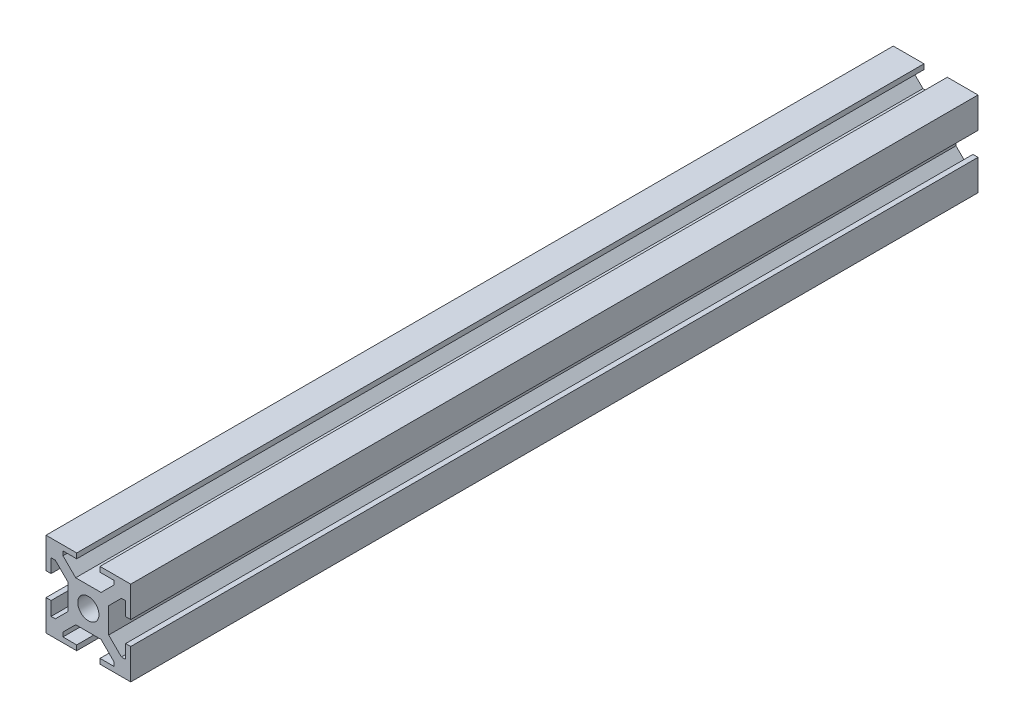
SolidWorks part; units mm, degrees
ref_plane "Plan de face" through (0, 0, 0) normal (0, 0, 1) x (1, 0, 0)
ref_plane "Plan de dessus" through (0, 0, 0) normal (0, 1, 0) x (1, 0, 0)
ref_plane "Plan de droite" through (0, 0, 0) normal (1, 0, 0) x (0, 0, -1)
sketch "Esquisse1" plane through (0, 0, 0) normal (0, 0, 1) x (1, 0, 0)
  line L1 (-22.5051, 0.0904) -> (-2.5051, 0.0904)
  line L2 (-22.5051, 0.0904) -> (-22.5051, -19.9096)
  line L3 (-22.5051, -19.9096) -> (-2.5051, -19.9096)
  line L4 (-2.5051, 0.0904) -> (-2.5051, -19.9096)
  dimension "D1" = 20
  dimension "D2" = 20
extrude "Boss.-Extru.1" add sketch "Esquisse1" along normal blind 200
sketch "Esquisse2" plane through (0, 0, 200) normal (0, 0, 1) x (1, 0, 0)
  line L0 (-22.5051, 0.0904) -> (-22.5051, -19.9096) construction
  line L1 (-22.5051, -7.1596) -> (-21.3051, -7.1596)
  line L2 (-22.5051, -7.1596) -> (-22.5051, -12.6596)
  line L3 (-22.5051, -12.6596) -> (-21.3051, -12.6596)
  line L4 (-21.3051, -7.1596) -> (-21.3051, -12.6596)
  line L5 (-2.5051, 0.0904) -> (-22.5051, 0.0904) construction
  line L6 (-15.2551, 0.0904) -> (-9.7551, 0.0904)
  line L7 (-15.2551, 0.0904) -> (-15.2551, -1.1096)
  line L8 (-15.2551, -1.1096) -> (-9.7551, -1.1096)
  line L9 (-9.7551, 0.0904) -> (-9.7551, -1.1096)
  line L10 (-2.5051, -19.9096) -> (-2.5051, 0.0904) construction
  line L11 (-2.5051, -7.1596) -> (-3.7051, -7.1596)
  line L12 (-2.5051, -7.1596) -> (-2.5051, -12.6596)
  line L13 (-2.5051, -12.6596) -> (-3.7051, -12.6596)
  line L14 (-3.7051, -7.1596) -> (-3.7051, -12.6596)
  line L15 (-22.5051, -19.9096) -> (-2.5051, -19.9096) construction
  line L16 (-15.2551, -19.9096) -> (-9.7551, -19.9096)
  line L17 (-15.2551, -19.9096) -> (-15.2551, -18.7096)
  line L18 (-15.2551, -18.7096) -> (-9.7551, -18.7096)
  line L19 (-9.7551, -19.9096) -> (-9.7551, -18.7096)
  dimension "D1" = 1.2
  dimension "D2" = 1.2
  dimension "D3" = 1.2
  dimension "D4" = 1.2
  dimension "D5" = 5.5
  dimension "D6" = 5.5
  dimension "D7" = 5.5
  dimension "D8" = 5.5
  dimension "D9" = 7.25
  dimension "D10" = 7.25
  dimension "D11" = 7.25
  dimension "D12" = 7.25
extrude "Enlèv. mat.-Extru.1" cut sketch "Esquisse2" against normal through all
sketch "Esquisse3" plane through (0, 0, 200) normal (0, 0, 1) x (1, 0, 0)
  line L0 (-15.2551, 0.0904) -> (-22.5051, 0.0904) construction
  line L1 (-21.3051, -15.9096) -> (-20.3051, -15.9096)
  line L2 (-21.3051, -15.9096) -> (-21.3051, -3.9096)
  line L3 (-21.3051, -3.9096) -> (-20.3051, -3.9096)
  line L4 (-17.3051, -12.9096) -> (-17.3051, -6.9096)
  line L5 (-18.5051, -1.1096) -> (-6.5051, -1.1096)
  line L6 (-18.5051, -1.1096) -> (-18.5051, -2.1096)
  line L7 (-15.5051, -5.1096) -> (-9.5051, -5.1096)
  line L8 (-6.5051, -1.1096) -> (-6.5051, -2.1096)
  line L9 (-3.7051, -3.9096) -> (-4.7051, -3.9096)
  line L10 (-3.7051, -3.9096) -> (-3.7051, -15.9096)
  line L11 (-3.7051, -15.9096) -> (-4.7051, -15.9096)
  line L12 (-7.7051, -6.9096) -> (-7.7051, -12.9096)
  line L13 (-6.5051, -18.7096) -> (-18.5051, -18.7096)
  line L14 (-6.5051, -18.7096) -> (-6.5051, -17.7096)
  line L15 (-9.5051, -14.7096) -> (-15.5051, -14.7096)
  line L16 (-18.5051, -18.7096) -> (-18.5051, -17.7096)
  line L17 (-2.5051, -7.1596) -> (-2.5051, 0.0904) construction
  line L18 (-15.2551, -1.1096) -> (-9.7551, -1.1096) construction
  line L19 (-3.7051, -7.1596) -> (-3.7051, -12.6596) construction
  line L20 (-9.7551, -19.9096) -> (-2.5051, -19.9096) construction
  line L21 (-22.5051, -12.6596) -> (-22.5051, -19.9096) construction
  line L22 (-22.5051, -19.9096) -> (-15.2551, -19.9096) construction
  line L23 (-15.5051, -14.7096) -> (-18.5051, -17.7096)
  line L24 (-20.3051, -15.9096) -> (-17.3051, -12.9096)
  line L25 (-6.5051, -17.7096) -> (-9.5051, -14.7096)
  line L26 (-4.7051, -15.9096) -> (-7.7051, -12.9096)
  line L27 (-4.7051, -3.9096) -> (-7.7051, -6.9096)
  line L28 (-9.5051, -5.1096) -> (-6.5051, -2.1096)
  line L29 (-18.5051, -2.1096) -> (-15.5051, -5.1096)
  line L30 (-20.3051, -3.9096) -> (-17.3051, -6.9096)
  point P1 (-17.3051, -3.9096)
  point P3 (-17.3051, -15.9096)
  point P5 (-6.5051, -5.1096)
  point P6 (-18.5051, -5.1096)
  point P9 (-7.7051, -15.9096)
  point P11 (-7.7051, -3.9096)
  point P13 (-18.5051, -14.7096)
  point P14 (-6.5051, -14.7096)
  point P24 (-6.1301, -19.9096)
  dimension "D1" = 4
  dimension "D2" = 4
  dimension "D3" = 4
  dimension "D4" = 4
  dimension "D5" = 12
  dimension "D6" = 4
  dimension "D7" = 12
  dimension "D8" = 4
  dimension "D9" = 0
  dimension "D10" = 0
  dimension "D11" = 4
  dimension "D12" = 12
  dimension "D13" = 12
  dimension "D14" = 4
  dimension "D15" = 1.2
  dimension "D16" = 1.2
  dimension "D17" = 3
  dimension "D18" = 3
  dimension "D19" = 3
  dimension "D20" = 3
  dimension "D21" = 3
  dimension "D22" = 3
  dimension "D23" = 3
  dimension "D24" = 3
  dimension "D25" = 3
  dimension "D26" = 3
  dimension "D27" = 3
  dimension "D28" = 3
  dimension "D29" = 3
  dimension "D30" = 3
  dimension "D31" = 3
  dimension "D32" = 3
extrude "Enlèv. mat.-Extru.2" cut sketch "Esquisse3" against normal through all
sketch "Esquisse4" plane through (0, 0, 200) normal (0, 0, 1) x (1, 0, 0)
  line L0 (-15.5051, -5.1096) -> (-9.5051, -5.1096) construction
  line L2 (-17.3051, -12.9096) -> (-17.3051, -6.9096) construction
  circle A0 centre (-12.5051, -9.9096) radius 2.5
  dimension "D1" = 5
  dimension "D2" = 4.8
  dimension "D3" = 4.8
extrude "Enlèv. mat.-Extru.3" cut sketch "Esquisse4" against normal through all
